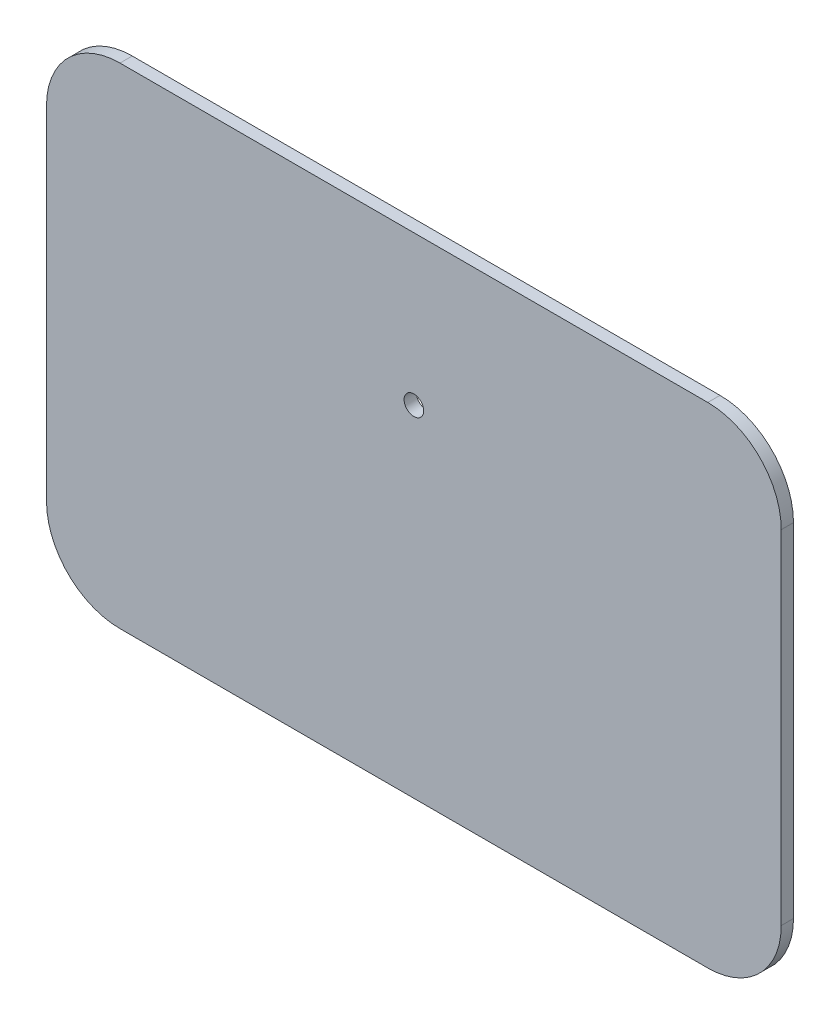
SolidWorks part; units mm, degrees
ref_plane "Alzado" through (0, 0, 0) normal (0, 0, 1) x (1, 0, 0)
ref_plane "Planta" through (0, 0, 0) normal (0, 1, 0) x (1, 0, 0)
ref_plane "Vista lateral" through (0, 0, 0) normal (1, 0, 0) x (0, 0, -1)
sketch "Croquis1" plane through (0, 0, 0) normal (0, 0, 1) x (1, 0, 0)
  line L0 (147.2417, -53.8378) -> (147.2417, 86.1622)
  line L1 (117.2417, 116.1622) -> (-122.7583, 116.1622)
  line L2 (-152.7583, 86.1622) -> (-152.7583, -53.8378)
  line L3 (-122.7583, -83.8378) -> (117.2417, -83.8378)
  line L4 (14.45, 52.0037) -> (80.39, 52.0037) construction
  line L7 (-1.61, 0.0037) -> (52.39, 0.0037) construction
  arc A0 (117.2417, -83.8378) -> (147.2417, -53.8378) centre (117.2417, -53.8378) ccw
  arc A1 (147.2417, 86.1622) -> (117.2417, 116.1622) centre (117.2417, 86.1622) ccw
  arc A2 (-122.7583, 116.1622) -> (-152.7583, 86.1622) centre (-122.7583, 86.1622) ccw
  arc A3 (-152.7583, -53.8378) -> (-122.7583, -83.8378) centre (-122.7583, -53.8378) ccw
  circle A4 centre (-1.61, 0.0037) radius 2
  circle A5 centre (52.39, 0.0037) radius 2
  circle A6 centre (102.39, 104.0037) radius 2
  circle A7 centre (-1.61, 104.0037) radius 2
  circle A8 centre (14.45, 52.0037) radius 10
  circle A9 centre (80.39, 52.0037) radius 4.05
  dimension "D1" = 4
  dimension "D2" = 4
  dimension "D3" = 30
  dimension "D13" = 16.06
  dimension "D15" = 20
  dimension "D16" = 8.1
  dimension "D4" = 52.39
  dimension "D5" = 102.39
  dimension "D6" = 147.2417
  dimension "D7" = 1.61
  dimension "D8" = 152.7583
  dimension "D9" = 0.0037
  dimension "D10" = 104.0037
  dimension "D11" = 116.1622
  dimension "D12" = 83.8378
  dimension "D14" = 52
  dimension "D17" = 65.94
extrude "Saliente-Extruir1" add sketch "Croquis1" along normal blind 5 contours L2 A3 L3 A0 L0 A1 L1 A2 A9 A8 A7 A6 A5 A4 | A7 | A6 | A5 | A4 | A8 | A9
sketch "Croquis3" [suppressed] plane through (0, 0, 0) normal (0, 0, -1) x (-1, 0, 0)
  line L0 (18.5999, 116.1622) -> (18.5999, 84.0612)
  line L1 (18.5999, 84.0612) -> (45.8446, 84.0612)
  line L2 (45.8446, 84.0612) -> (45.8446, 36.9657)
  line L3 (45.8446, 36.9657) -> (91.4684, 36.9657)
  line L4 (-117.2417, -83.8378) -> (122.7583, -83.8378)
  line L5 (152.7583, -53.8378) -> (152.7583, 86.1622)
  line L6 (122.7583, 116.1622) -> (-117.2417, 116.1622)
  line L7 (-147.2417, 86.1622) -> (-147.2417, -53.8378)
  line L8 (-117.2417, -83.8378) -> (122.7583, -83.8378)
  line L9 (152.7583, -53.8378) -> (152.7583, 86.1622)
  line L10 (122.7583, 116.1622) -> (-117.2417, 116.1622)
  line L11 (-147.2417, 86.1622) -> (-147.2417, -53.8378)
  line L12 (91.4684, 36.9657) -> (91.4684, 116.1622)
  line L13 (-31.5686, -83.8378) -> (-31.5686, -12.1903)
  line L14 (-31.5686, -12.1903) -> (43.7842, -12.1903)
  line L15 (152.7583, -29.2624) -> (95.0006, -29.2624)
  line L16 (95.0006, -29.2624) -> (95.0006, 9.5914)
  line L17 (95.0006, 9.5914) -> (43.7842, 9.5914)
  line L18 (43.7842, 9.5914) -> (43.7842, -12.1903)
  arc A4 (-147.2417, -53.8378) -> (-117.2417, -83.8378) centre (-117.2417, -53.8378) ccw
  arc A5 (122.7583, -83.8378) -> (152.7583, -53.8378) centre (122.7583, -53.8378) ccw
  arc A6 (152.7583, 86.1622) -> (122.7583, 116.1622) centre (122.7583, 86.1622) ccw
  arc A7 (-117.2417, 116.1622) -> (-147.2417, 86.1622) centre (-117.2417, 86.1622) ccw
  arc A8 (-147.2417, -53.8378) -> (-117.2417, -83.8378) centre (-117.2417, -53.8378) ccw
  arc A9 (122.7583, -83.8378) -> (152.7583, -53.8378) centre (122.7583, -53.8378) ccw
  arc A10 (152.7583, 86.1622) -> (122.7583, 116.1622) centre (122.7583, 86.1622) ccw
  arc A11 (-117.2417, 116.1622) -> (-147.2417, 86.1622) centre (-117.2417, 86.1622) ccw
  dimension "D1" = 0
sketch "Croquis4" plane through (0, 0, 0) normal (0, 0, -1) x (-1, 0, 0)
  line L2 (-117.2417, 116.1622) -> (122.7583, 116.1622) construction
  line L3 (-147.2417, -53.8378) -> (-147.2417, 86.1622) construction
  circle A0 centre (2.7583, 55.1622) radius 4
  dimension "D1" = 8
  dimension "D2" = 61
  dimension "D3" = 150
extrude "Cortar-Extruir2" cut sketch "Croquis4" against normal blind 10 contours A0
